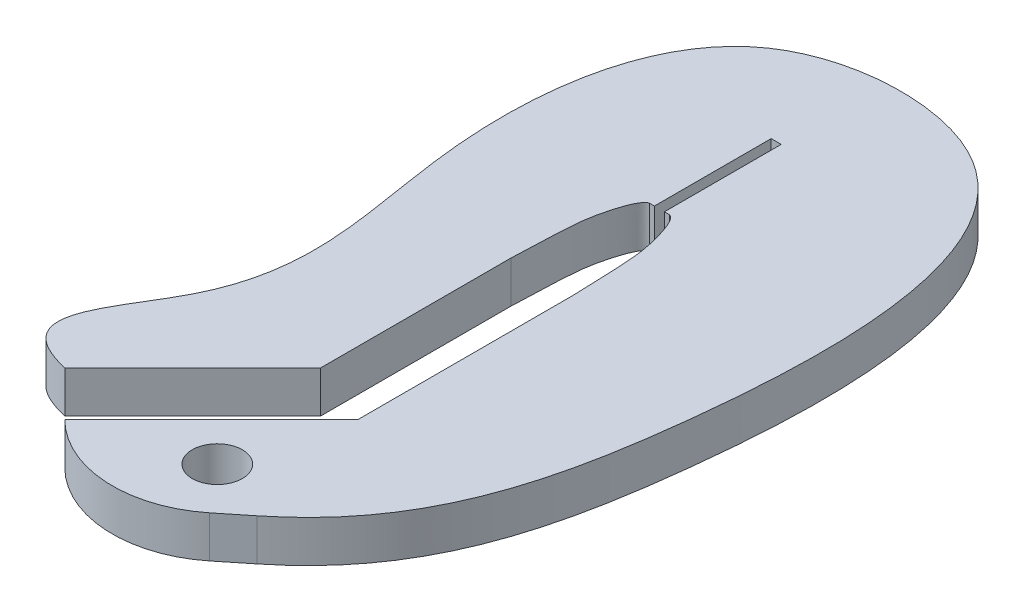
SolidWorks part; units mm, degrees
ref_plane "Front Plane" through (0, 0, 0) normal (0, 0, 1) x (1, 0, 0)
ref_plane "Top Plane" through (0, 0, 0) normal (0, 1, 0) x (1, 0, 0)
ref_plane "Right Plane" through (0, 0, 0) normal (1, 0, 0) x (0, 0, -1)
sketch "Sketch1" plane through (0, 0, 0) normal (0, 1, 0) x (1, 0, 0)
  line L0 (0.6, 0.6) -> (0.6, 12)
  line L1 (1.9, 19) -> (2.2, 19)
  line L2 (2.8, 19) -> (3.1, 19)
  line L3 (0.6, 0.6) -> (-7.0711, -7.0711)
  line L4 (4.4, 12) -> (4.4, -0.974)
  line L5 (2.2, 26) -> (2.8, 26)
  line L6 (4.4, -0.974) -> (-4.3841, -9.7581)
  line L7 (0, 0) -> (-7.0711, -7.0711) construction
  line L8 (2.687, -2.687) -> (-4.3841, -9.7581) construction
  line L11 (2.8, 19) -> (2.8, 26)
  line L12 (2.2, 19) -> (2.2, 26)
  circle A0 centre (2.5, -7.5) radius 1.5
  arc A1 (-4.3841, -9.7581) -> (4.7979, -10.2533) centre (0.4827, -4.8913) ccw
  arc A2 (6.3677, -8.9913) -> (4.7979, -10.2533) centre (1258.713, -1568.3601) ccw
  spline S0 degree 3 poles (6.3677, -8.9913) (8.3359, -7.4105) (12.4423, -2.4758) (15.2743, 11.3721) (15.3996, 33.1917) (-6.2023, 32.4691) (-8.069, 15.0563) (-3.3711, 2.7664) (-12.0213, -5.9328) (-7.0711, -7.0711) knots 0.011628 0.011628 0.011628 0.011628 0.081878 0.22072 0.462999 0.579337 0.740821 0.900193 1 1 1 1
  spline S1 degree 3 poles (0.6, 12) (0.7059, 15.5317) (0.8303, 16.2001) (0.9633, 16.9798) (1.429, 18.8963) (1.9, 19) knots 0 0 0 0 0.421521 0.521521 1 1 1 1
  spline S2 degree 3 poles (4.4, 12) (4.2941, 15.5317) (4.1697, 16.2001) (4.0367, 16.9798) (3.571, 18.8963) (3.1, 19) knots 0 0 0 0 0.421521 0.521521 1 1 1 1
extrude "Boss-Extrude1" add sketch "Sketch1" along normal blind 2.5
